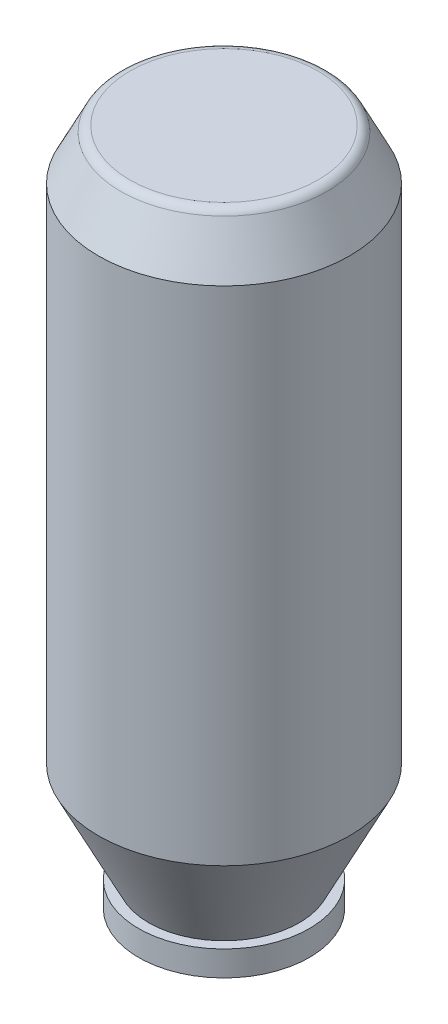
SolidWorks part; units mm, degrees
ref_plane "前视基准面" through (0, 0, 0) normal (0, 0, 1) x (1, 0, 0)
ref_plane "上视基准面" through (0, 0, 0) normal (0, 1, 0) x (1, 0, 0)
ref_plane "右视基准面" through (0, 0, 0) normal (1, 0, 0) x (0, 0, -1)
sketch "草图2" plane through (0, 0, 0) normal (1, 0, 0) x (0, 0, -1)
  line L0 (0, 0) -> (25, 0)
  line L1 (0, 0) -> (0, 10)
  line L2 (0, 10) -> (20, 10)
  line L3 (20, 10) -> (25, 0)
  dimension "D1" = 10
  dimension "D2" = 25
  dimension "D3" = 20
revolve "旋转1" add sketch "草图2" angle 360 about L1
sketch "草图3" plane through (0, 0, 0) normal (0, -1, 0) x (-1, 0, 0)
  circle A0 centre (0, 0) radius 25
extrude "凸台-拉伸2" add sketch "草图3" along normal blind 100
sketch "草图5" plane through (0, 0, 0) normal (1, 0, 0) x (0, 0, -1)
  line L0 (-25, -100) -> (0, -100)
  line L1 (0, -100) -> (0, -120)
  line L2 (0, -120) -> (-15, -120)
  line L3 (-15, -120) -> (-25, -100)
  dimension "D1" = 15
  dimension "D2" = 20
revolve "旋转2" add sketch "草图5" angle 360 about L1
sketch "草图6" plane through (0, -120, 0) normal (0, -1, 0) x (-1, 0, 0)
  circle A0 centre (0, 0) radius 17
extrude "凸台-拉伸3" add sketch "草图6" along normal blind 5
fillet "圆角1" radius 2 1 edges at (0, 10, -20)
